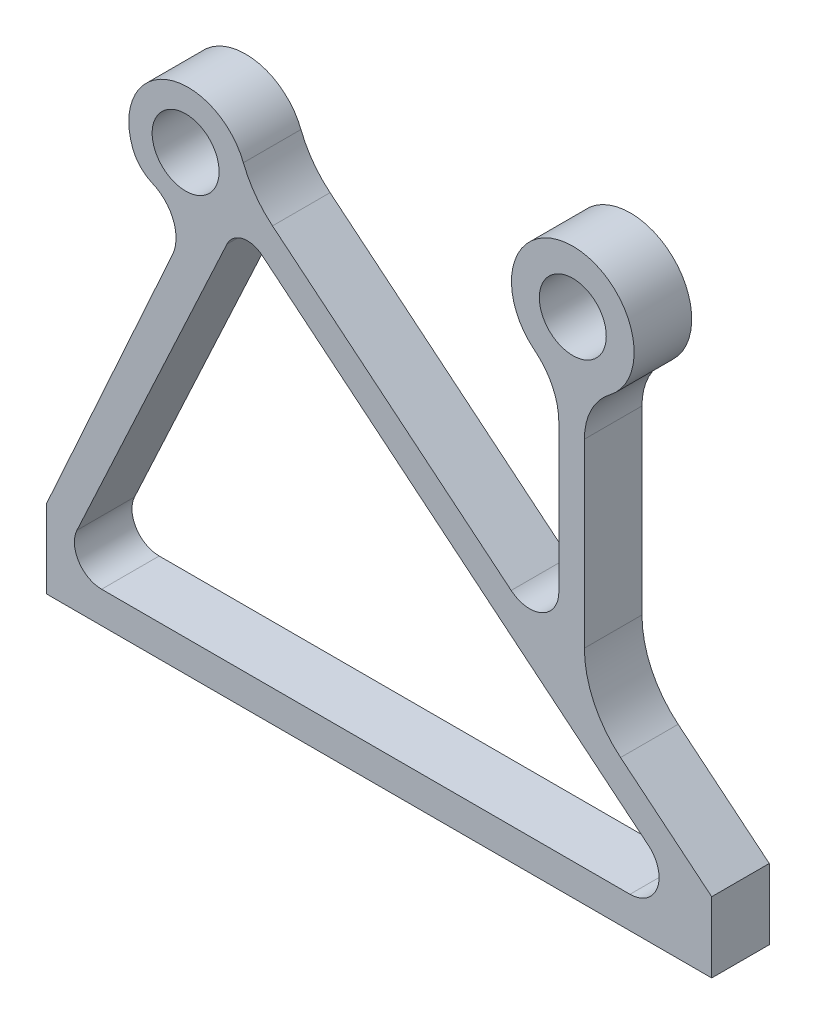
SolidWorks part; units mm, degrees
ref_plane "Front Plane" through (0, 0, 0) normal (0, 0, 1) x (1, 0, 0)
ref_plane "Top Plane" through (0, 0, 0) normal (0, 1, 0) x (1, 0, 0)
ref_plane "Right Plane" through (0, 0, 0) normal (1, 0, 0) x (0, 0, -1)
sketch "Szkic1" [suppressed] plane through (0, 0, 0) normal (0, 0, 1) x (1, 0, 0)
  line L1 (0, 0) -> (462, 0)
  line L2 (0, 0) -> (0, 400)
  line L3 (0, 400) -> (462, 400)
  line L4 (462, 0) -> (462, 400)
  circle A0 centre (96.5, 314) radius 23.25
  circle A1 centre (365.5, 349.5) radius 23.25
  dimension "D3" = 46.5
  dimension "D1" = 400
  dimension "D2" = 462
  dimension "D4" = 269
  dimension "D5" = 96.5
  dimension "D6" = 314
  dimension "D7" = 349.5
extrude "Dodanie-wyciągnięcie1" [suppressed] add sketch "Szkic1" along normal blind 40
other "Grafika1" [suppressed]
other "Grafika (Zamknięta) -1" [suppressed]
other "Grafika (Zamknięta) -2" [suppressed]
other "Grafika (Zamknięta) -3" [suppressed]
other "Grafika (Zamknięta) -4" [suppressed]
other "Grafika (Zamknięta) -5" [suppressed]
other "Grafika (Zamknięta) -6" [suppressed]
sketch "Szkic2" plane through (0, 0, 0) normal (0, 0, 1) x (1, 0, 0)
  line L0 (0, 0) -> (0, 54.6889)
  line L1 (0, 54.6889) -> (87.4534, 248.0675)
  line L2 (156.8568, 299.9573) -> (322.6845, 163.5273)
  line L3 (355.7939, 179.1622) -> (355.7939, 281.2537)
  line L4 (373.5508, 279.9685) -> (373.5508, 154.2281)
  line L5 (398.6868, 100.9986) -> (462, 48.9095)
  line L6 (462, 48.9095) -> (462, 0)
  line L7 (462, 0) -> (0, 0)
  line L8 (38.1405, 21.9857) -> (405.2316, 21.9857)
  line L9 (418.0699, 57.7974) -> (149.5735, 278.6951)
  line L10 (125.2039, 273.1516) -> (20.9832, 48.878)
  circle A0 centre (96.5, 314) radius 23.25
  circle A1 centre (365.5, 349.5) radius 23.25
  arc A2 (87.4534, 248.0675) -> (73.4484, 283.8616) centre (62.9877, 259.1318) ccw
  arc A3 (73.4484, 283.8616) -> (59.808, 297.9212) centre (83.2387, 307.0066) cw
  arc A4 (59.808, 297.9212) -> (136.6262, 327.8418) centre (98.2398, 312.8233) cw
  arc A8 (322.6845, 163.5273) -> (355.7939, 179.1622) centre (335.5477, 179.1622) ccw
  arc A9 (355.7939, 281.2537) -> (338.9638, 316.1583) centre (311.1837, 281.2537) ccw
  arc A10 (338.9638, 316.1583) -> (391.2275, 315.5304) centre (365.5, 349.5) cw
  arc A11 (373.5508, 154.2281) -> (398.6868, 100.9986) centre (442.4798, 154.2281) ccw
  arc A12 (391.2275, 315.5304) -> (373.5508, 279.9685) centre (418.161, 279.9685) ccw
  arc A13 (405.2316, 21.9857) -> (418.0699, 57.7974) centre (405.2316, 42.1927) ccw
  arc A14 (149.5735, 278.6951) -> (125.2039, 273.1516) centre (139.534, 266.4923) ccw
  arc A15 (20.9832, 48.878) -> (38.1405, 21.9857) centre (38.1405, 40.905) ccw
  arc A16 (136.6262, 327.8418) -> (156.8568, 299.9573) centre (200.2907, 352.7503) ccw
  point P14 (136.1836, 328.9275)
  point P16 (87.4534, 248.0675)
  point P17 (405.2316, 21.9857)
  point P18 (312.8559, 176.6644)
  point P26 (0, 0)
  point P46 (355.3224, 192.8017)
  point P47 (0, 0)
  point P48 (311.1837, 281.2537)
  dimension "D1" = 46.5
  dimension "D2" = 314
  dimension "D3" = 269
  dimension "D4" = 349.5
  dimension "D5" = 96.5
extrude "Dodanie-wyciągnięcie2" add sketch "Szkic2" along normal blind 40
